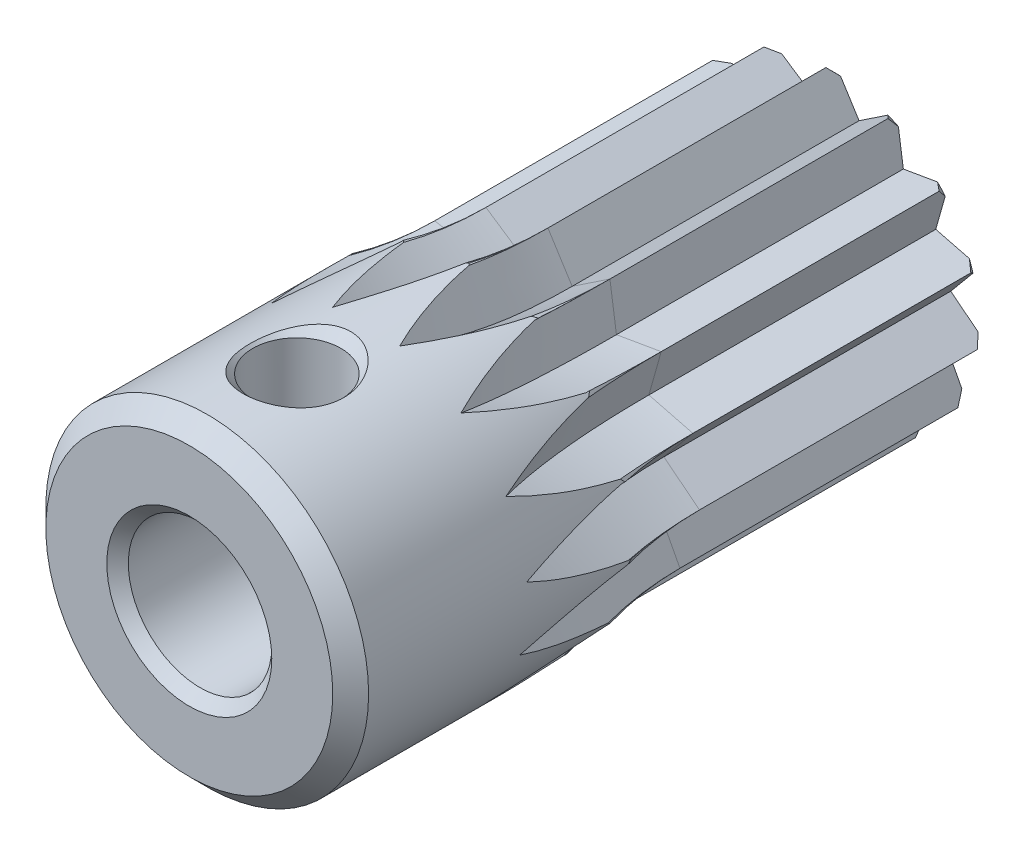
SolidWorks part; units mm, degrees
material "Delrin 2700 NC010, Low Viscosity Acetal Copolymer (SS)"
ref_plane "Front Plane" through (0, 0, 0) normal (0, 0, 1) x (1, 0, 0)
ref_plane "Top Plane" through (0, 0, 0) normal (0, 1, 0) x (1, 0, 0)
ref_plane "Right Plane" through (0, 0, 0) normal (1, 0, 0) x (0, 0, -1)
ref_plane "Plane1" through (0, 0, 0) normal (1, 0, 0) x (0, 0, -1)
sketch "Sketch1" plane through (0, 0, 0) normal (1, 0, 0) x (0, 0, -1)
  line L0 (-18, 2.3) -> (-17.7, 2)
  line L1 (-17.7, 2) -> (-0.3, 2)
  line L2 (-0.3, 2) -> (0, 2.3)
  line L3 (0, 2.3) -> (0, 4)
  line L4 (0, 4) -> (-0.5, 4.5)
  line L5 (-0.5, 4.5) -> (-17.5, 4.5)
  line L6 (-17.5, 4.5) -> (-18, 4)
  line L7 (-18, 4) -> (-18, 2.3)
  line L8 (0, 0) -> (-18, 0) construction
revolve "Revolve1" add sketch "Sketch1" angle 360 about L8
ref_plane "Plane2" through (0, 0, 8) normal (0, 0, 1) x (1, 0, 0)
sketch "Sketch2" plane through (0, 0, 8) normal (0, 0, 1) x (1, 0, 0)
  line L0 (-4.2267, -0.4442) -> (-3.0909, -1.0043)
  line L1 (-3.0909, -1.0043) -> (-3.6806, -2.125)
  line L2 (-3.6806, -2.125) -> (-2.4152, -2.1747)
  line L3 (-2.4152, -2.1747) -> (-2.4981, -3.4383)
  line L4 (-2.4981, -3.4383) -> (-1.3219, -2.969)
  line L5 (-1.3219, -2.969) -> (-0.8836, -4.1571)
  line L6 (-0.8836, -4.1571) -> (0, -3.25)
  line L7 (0, -3.25) -> (0.8836, -4.1571)
  line L8 (0.8836, -4.1571) -> (1.3219, -2.969)
  line L9 (1.3219, -2.969) -> (2.4981, -3.4383)
  line L10 (2.4981, -3.4383) -> (2.4152, -2.1747)
  line L11 (2.4152, -2.1747) -> (3.6806, -2.125)
  line L12 (3.6806, -2.125) -> (3.0909, -1.0043)
  line L13 (3.0909, -1.0043) -> (4.2267, -0.4442)
  line L14 (4.2267, -0.4442) -> (3.2322, 0.3397)
  line L15 (3.2322, 0.3397) -> (4.042, 1.3133)
  line L16 (4.042, 1.3133) -> (2.8146, 1.625)
  line L17 (2.8146, 1.625) -> (3.1584, 2.8438)
  line L18 (3.1584, 2.8438) -> (1.9103, 2.6293)
  line L19 (1.9103, 2.6293) -> (1.7286, 3.8826)
  line L20 (1.7286, 3.8826) -> (0.6757, 3.179)
  line L21 (0.6757, 3.179) -> (0, 4.25)
  line L22 (0, 4.25) -> (-0.6757, 3.179)
  line L23 (-0.6757, 3.179) -> (-1.7286, 3.8826)
  line L24 (-1.7286, 3.8826) -> (-1.9103, 2.6293)
  line L25 (-1.9103, 2.6293) -> (-3.1584, 2.8438)
  line L26 (-3.1584, 2.8438) -> (-2.8146, 1.625)
  line L27 (-2.8146, 1.625) -> (-4.042, 1.3133)
  line L28 (-4.042, 1.3133) -> (-3.2322, 0.3397)
  line L29 (-3.2322, 0.3397) -> (-4.2267, -0.4442)
  circle A0 centre (0, 0) radius 8.5
extrude "Cut-Extrude1" cut sketch "Sketch2" against normal blind 8
ref_plane "Plane3" through (0, 0, 8) normal (0, 0, 1) x (1, 0, 0)
sketch "Sketch3" plane through (0, 0, 8) normal (0, 0, 1) x (1, 0, 0)
  line L0 (-2.0791, 14.0315) -> (0, 4.25)
  line L1 (0, 4.25) -> (-0.6757, 3.179)
  line L2 (-0.6757, 3.179) -> (-1.7286, 3.8826)
  line L3 (-1.7286, 3.8826) -> (-3.8077, 13.664)
  line L4 (-3.8077, 13.664) -> (-2.0791, 14.0315)
  line L5 (-3.8077, 13.664) -> (-2.0791, 14.0315) construction
revolve "Cut-Revolve1" cut sketch "Sketch3" angle 360 about L5
ref_plane "Plane4" through (0, 0, 8) normal (0, 0, 1) x (1, 0, 0)
sketch "Sketch4" plane through (0, 0, 8) normal (0, 0, 1) x (1, 0, 0)
  line L0 (3.8077, 13.664) -> (1.7286, 3.8826)
  line L1 (1.7286, 3.8826) -> (0.6757, 3.179)
  line L2 (0.6757, 3.179) -> (0, 4.25)
  line L3 (0, 4.25) -> (2.0791, 14.0315)
  line L4 (2.0791, 14.0315) -> (3.8077, 13.664)
  line L5 (2.0791, 14.0315) -> (3.8077, 13.664) construction
revolve "Cut-Revolve2" cut sketch "Sketch4" angle 360 about L5
ref_plane "Plane5" through (0, 0, 8) normal (0, 0, 1) x (1, 0, 0)
sketch "Sketch5" plane through (0, 0, 8) normal (0, 0, 1) x (1, 0, 0)
  line L0 (9.0362, 10.934) -> (3.1584, 2.8438)
  line L1 (3.1584, 2.8438) -> (1.9103, 2.6293)
  line L2 (1.9103, 2.6293) -> (1.7286, 3.8826)
  line L3 (1.7286, 3.8826) -> (7.6065, 11.9727)
  line L4 (7.6065, 11.9727) -> (9.0362, 10.934)
  line L5 (7.6065, 11.9727) -> (9.0362, 10.934) construction
revolve "Cut-Revolve3" cut sketch "Sketch5" angle 360 about L5
ref_plane "Plane6" through (0, 0, 8) normal (0, 0, 1) x (1, 0, 0)
sketch "Sketch6" plane through (0, 0, 8) normal (0, 0, 1) x (1, 0, 0)
  line L0 (12.7022, 6.3133) -> (4.042, 1.3133)
  line L1 (4.042, 1.3133) -> (2.8146, 1.625)
  line L2 (2.8146, 1.625) -> (3.1584, 2.8438)
  line L3 (3.1584, 2.8438) -> (11.8186, 7.8438)
  line L4 (11.8186, 7.8438) -> (12.7022, 6.3133)
  line L5 (11.8186, 7.8438) -> (12.7022, 6.3133) construction
revolve "Cut-Revolve4" cut sketch "Sketch6" angle 360 about L5
ref_plane "Plane7" through (0, 0, 8) normal (0, 0, 1) x (1, 0, 0)
sketch "Sketch7" plane through (0, 0, 8) normal (0, 0, 1) x (1, 0, 0)
  line L0 (14.1719, 0.601) -> (4.2267, -0.4442)
  line L1 (4.2267, -0.4442) -> (3.2322, 0.3397)
  line L2 (3.2322, 0.3397) -> (4.042, 1.3133)
  line L3 (4.042, 1.3133) -> (13.9872, 2.3586)
  line L4 (13.9872, 2.3586) -> (14.1719, 0.601)
  line L5 (13.9872, 2.3586) -> (14.1719, 0.601) construction
revolve "Cut-Revolve5" cut sketch "Sketch7" angle 360 about L5
ref_plane "Plane8" through (0, 0, 8) normal (0, 0, 1) x (1, 0, 0)
sketch "Sketch8" plane through (0, 0, 8) normal (0, 0, 1) x (1, 0, 0)
  line L0 (13.1912, -5.2152) -> (3.6806, -2.125)
  line L1 (3.6806, -2.125) -> (3.0909, -1.0043)
  line L2 (3.0909, -1.0043) -> (4.2267, -0.4442)
  line L3 (4.2267, -0.4442) -> (13.7373, -3.5344)
  line L4 (13.7373, -3.5344) -> (13.1912, -5.2152)
  line L5 (13.7373, -3.5344) -> (13.1912, -5.2152) construction
revolve "Cut-Revolve6" cut sketch "Sketch8" angle 360 about L5
ref_plane "Plane9" through (0, 0, 8) normal (0, 0, 1) x (1, 0, 0)
sketch "Sketch9" plane through (0, 0, 8) normal (0, 0, 1) x (1, 0, 0)
  line L0 (9.9295, -10.1296) -> (2.4981, -3.4383)
  line L1 (2.4981, -3.4383) -> (2.4152, -2.1747)
  line L2 (2.4152, -2.1747) -> (3.6806, -2.125)
  line L3 (3.6806, -2.125) -> (11.1121, -8.8163)
  line L4 (11.1121, -8.8163) -> (9.9295, -10.1296)
  line L5 (11.1121, -8.8163) -> (9.9295, -10.1296) construction
revolve "Cut-Revolve7" cut sketch "Sketch9" angle 360 about L5
ref_plane "Plane10" through (0, 0, 8) normal (0, 0, 1) x (1, 0, 0)
sketch "Sketch10" plane through (0, 0, 8) normal (0, 0, 1) x (1, 0, 0)
  line L0 (4.951, -13.2926) -> (0.8836, -4.1571)
  line L1 (0.8836, -4.1571) -> (1.3219, -2.969)
  line L2 (1.3219, -2.969) -> (2.4981, -3.4383)
  line L3 (2.4981, -3.4383) -> (6.5655, -12.5738)
  line L4 (6.5655, -12.5738) -> (4.951, -13.2926)
  line L5 (6.5655, -12.5738) -> (4.951, -13.2926) construction
revolve "Cut-Revolve8" cut sketch "Sketch10" angle 360 about L5
ref_plane "Plane11" through (0, 0, 8) normal (0, 0, 1) x (1, 0, 0)
sketch "Sketch11" plane through (0, 0, 8) normal (0, 0, 1) x (1, 0, 0)
  line L0 (-0.8836, -14.1571) -> (-0.8836, -4.1571)
  line L1 (-0.8836, -4.1571) -> (0, -3.25)
  line L2 (0, -3.25) -> (0.8836, -4.1571)
  line L3 (0.8836, -4.1571) -> (0.8836, -14.1571)
  line L4 (0.8836, -14.1571) -> (-0.8836, -14.1571)
  line L5 (0.8836, -14.1571) -> (-0.8836, -14.1571) construction
revolve "Cut-Revolve9" cut sketch "Sketch11" angle 360 about L5
ref_plane "Plane12" through (0, 0, 8) normal (0, 0, 1) x (1, 0, 0)
sketch "Sketch12" plane through (0, 0, 8) normal (0, 0, 1) x (1, 0, 0)
  line L0 (-6.5655, -12.5738) -> (-2.4981, -3.4383)
  line L1 (-2.4981, -3.4383) -> (-1.3219, -2.969)
  line L2 (-1.3219, -2.969) -> (-0.8836, -4.1571)
  line L3 (-0.8836, -4.1571) -> (-4.951, -13.2926)
  line L4 (-4.951, -13.2926) -> (-6.5655, -12.5738)
  line L5 (-4.951, -13.2926) -> (-6.5655, -12.5738) construction
revolve "Cut-Revolve10" cut sketch "Sketch12" angle 360 about L5
ref_plane "Plane13" through (0, 0, 8) normal (0, 0, 1) x (1, 0, 0)
sketch "Sketch13" plane through (0, 0, 8) normal (0, 0, 1) x (1, 0, 0)
  line L0 (-11.1121, -8.8163) -> (-3.6806, -2.125)
  line L1 (-3.6806, -2.125) -> (-2.4152, -2.1747)
  line L2 (-2.4152, -2.1747) -> (-2.4981, -3.4383)
  line L3 (-2.4981, -3.4383) -> (-9.9295, -10.1296)
  line L4 (-9.9295, -10.1296) -> (-11.1121, -8.8163)
  line L5 (-9.9295, -10.1296) -> (-11.1121, -8.8163) construction
revolve "Cut-Revolve11" cut sketch "Sketch13" angle 360 about L5
ref_plane "Plane14" through (0, 0, 8) normal (0, 0, 1) x (1, 0, 0)
sketch "Sketch14" plane through (0, 0, 8) normal (0, 0, 1) x (1, 0, 0)
  line L0 (-13.7373, -3.5344) -> (-4.2267, -0.4442)
  line L1 (-4.2267, -0.4442) -> (-3.0909, -1.0043)
  line L2 (-3.0909, -1.0043) -> (-3.6806, -2.125)
  line L3 (-3.6806, -2.125) -> (-13.1912, -5.2152)
  line L4 (-13.1912, -5.2152) -> (-13.7373, -3.5344)
  line L5 (-13.1912, -5.2152) -> (-13.7373, -3.5344) construction
revolve "Cut-Revolve12" cut sketch "Sketch14" angle 360 about L5
ref_plane "Plane15" through (0, 0, 8) normal (0, 0, 1) x (1, 0, 0)
sketch "Sketch15" plane through (0, 0, 8) normal (0, 0, 1) x (1, 0, 0)
  line L0 (-13.9872, 2.3586) -> (-4.042, 1.3133)
  line L1 (-4.042, 1.3133) -> (-3.2322, 0.3397)
  line L2 (-3.2322, 0.3397) -> (-4.2267, -0.4442)
  line L3 (-4.2267, -0.4442) -> (-14.1719, 0.601)
  line L4 (-14.1719, 0.601) -> (-13.9872, 2.3586)
  line L5 (-14.1719, 0.601) -> (-13.9872, 2.3586) construction
revolve "Cut-Revolve13" cut sketch "Sketch15" angle 360 about L5
ref_plane "Plane16" through (0, 0, 8) normal (0, 0, 1) x (1, 0, 0)
sketch "Sketch16" plane through (0, 0, 8) normal (0, 0, 1) x (1, 0, 0)
  line L0 (-11.8186, 7.8438) -> (-3.1584, 2.8438)
  line L1 (-3.1584, 2.8438) -> (-2.8146, 1.625)
  line L2 (-2.8146, 1.625) -> (-4.042, 1.3133)
  line L3 (-4.042, 1.3133) -> (-12.7022, 6.3133)
  line L4 (-12.7022, 6.3133) -> (-11.8186, 7.8438)
  line L5 (-12.7022, 6.3133) -> (-11.8186, 7.8438) construction
revolve "Cut-Revolve14" cut sketch "Sketch16" angle 360 about L5
ref_plane "Plane17" through (0, 0, 8) normal (0, 0, 1) x (1, 0, 0)
sketch "Sketch17" plane through (0, 0, 8) normal (0, 0, 1) x (1, 0, 0)
  line L0 (-7.6065, 11.9727) -> (-1.7286, 3.8826)
  line L1 (-1.7286, 3.8826) -> (-1.9103, 2.6293)
  line L2 (-1.9103, 2.6293) -> (-3.1584, 2.8438)
  line L3 (-3.1584, 2.8438) -> (-9.0362, 10.934)
  line L4 (-9.0362, 10.934) -> (-7.6065, 11.9727)
  line L5 (-9.0362, 10.934) -> (-7.6065, 11.9727) construction
revolve "Cut-Revolve15" cut sketch "Sketch17" angle 360 about L5
ref_plane "Plane18" through (0, 0, 8) normal (0, 0, 1) x (1, 0, 0)
sketch "Sketch18" plane through (0, 0, 8) normal (0, 0, 1) x (1, 0, 0)
  line L0 (-1.8835, 14.0731) -> (0.1956, 4.2916)
  line L1 (0.1956, 4.2916) -> (0, 4.25)
  line L2 (0, 4.25) -> (-0.6757, 3.179)
  line L3 (-0.6757, 3.179) -> (-1.7286, 3.8826)
  line L4 (-1.7286, 3.8826) -> (-1.9243, 3.841)
  line L5 (-1.9243, 3.841) -> (-4.0034, 13.6225)
  line L6 (-4.0034, 13.6225) -> (-1.8835, 14.0731)
  line L7 (-4.0034, 13.6225) -> (-1.8835, 14.0731) construction
revolve "Cut-Revolve16" cut sketch "Sketch18" angle 360 about L7
ref_plane "Plane19" through (0, 0, 8) normal (0, 0, 1) x (1, 0, 0)
sketch "Sketch19" plane through (0, 0, 8) normal (0, 0, 1) x (1, 0, 0)
  line L0 (4.0034, 13.6225) -> (1.9243, 3.841)
  line L1 (1.9243, 3.841) -> (1.7286, 3.8826)
  line L2 (1.7286, 3.8826) -> (0.6757, 3.179)
  line L3 (0.6757, 3.179) -> (0, 4.25)
  line L4 (0, 4.25) -> (-0.1956, 4.2916)
  line L5 (-0.1956, 4.2916) -> (1.8835, 14.0731)
  line L6 (1.8835, 14.0731) -> (4.0034, 13.6225)
  line L7 (1.8835, 14.0731) -> (4.0034, 13.6225) construction
revolve "Cut-Revolve17" cut sketch "Sketch19" angle 360 about L7
ref_plane "Plane20" through (0, 0, 8) normal (0, 0, 1) x (1, 0, 0)
sketch "Sketch20" plane through (0, 0, 8) normal (0, 0, 1) x (1, 0, 0)
  line L0 (12.8022, 6.1401) -> (4.142, 1.1401)
  line L1 (4.142, 1.1401) -> (4.042, 1.3133)
  line L2 (4.042, 1.3133) -> (2.8146, 1.625)
  line L3 (2.8146, 1.625) -> (3.1584, 2.8438)
  line L4 (3.1584, 2.8438) -> (3.0584, 3.017)
  line L5 (3.0584, 3.017) -> (11.7186, 8.017)
  line L6 (11.7186, 8.017) -> (12.8022, 6.1401)
  line L7 (11.7186, 8.017) -> (12.8022, 6.1401) construction
revolve "Cut-Revolve18" cut sketch "Sketch20" angle 360 about L7
ref_plane "Plane21" through (0, 0, 8) normal (0, 0, 1) x (1, 0, 0)
sketch "Sketch21" plane through (0, 0, 8) normal (0, 0, 1) x (1, 0, 0)
  line L0 (13.1294, -5.4054) -> (3.6188, -2.3152)
  line L1 (3.6188, -2.3152) -> (3.6806, -2.125)
  line L2 (3.6806, -2.125) -> (3.0909, -1.0043)
  line L3 (3.0909, -1.0043) -> (4.2267, -0.4442)
  line L4 (4.2267, -0.4442) -> (4.2885, -0.254)
  line L5 (4.2885, -0.254) -> (13.7991, -3.3442)
  line L6 (13.7991, -3.3442) -> (13.1294, -5.4054)
  line L7 (13.7991, -3.3442) -> (13.1294, -5.4054) construction
revolve "Cut-Revolve19" cut sketch "Sketch21" angle 360 about L7
ref_plane "Plane22" through (0, 0, 8) normal (0, 0, 1) x (1, 0, 0)
sketch "Sketch22" plane through (0, 0, 8) normal (0, 0, 1) x (1, 0, 0)
  line L0 (4.7683, -13.3739) -> (0.7009, -4.2385)
  line L1 (0.7009, -4.2385) -> (0.8836, -4.1571)
  line L2 (0.8836, -4.1571) -> (1.3219, -2.969)
  line L3 (1.3219, -2.969) -> (2.4981, -3.4383)
  line L4 (2.4981, -3.4383) -> (2.6808, -3.357)
  line L5 (2.6808, -3.357) -> (6.7482, -12.4924)
  line L6 (6.7482, -12.4924) -> (4.7683, -13.3739)
  line L7 (6.7482, -12.4924) -> (4.7683, -13.3739) construction
revolve "Cut-Revolve20" cut sketch "Sketch22" angle 360 about L7
ref_plane "Plane23" through (0, 0, 8) normal (0, 0, 1) x (1, 0, 0)
sketch "Sketch23" plane through (0, 0, 8) normal (0, 0, 1) x (1, 0, 0)
  line L0 (-6.7482, -12.4924) -> (-2.6808, -3.357)
  line L1 (-2.6808, -3.357) -> (-2.4981, -3.4383)
  line L2 (-2.4981, -3.4383) -> (-1.3219, -2.969)
  line L3 (-1.3219, -2.969) -> (-0.8836, -4.1571)
  line L4 (-0.8836, -4.1571) -> (-0.7009, -4.2385)
  line L5 (-0.7009, -4.2385) -> (-4.7683, -13.3739)
  line L6 (-4.7683, -13.3739) -> (-6.7482, -12.4924)
  line L7 (-4.7683, -13.3739) -> (-6.7482, -12.4924) construction
revolve "Cut-Revolve21" cut sketch "Sketch23" angle 360 about L7
ref_plane "Plane24" through (0, 0, 8) normal (0, 0, 1) x (1, 0, 0)
sketch "Sketch24" plane through (0, 0, 8) normal (0, 0, 1) x (1, 0, 0)
  line L0 (-13.7991, -3.3442) -> (-4.2885, -0.254)
  line L1 (-4.2885, -0.254) -> (-4.2267, -0.4442)
  line L2 (-4.2267, -0.4442) -> (-3.0909, -1.0043)
  line L3 (-3.0909, -1.0043) -> (-3.6806, -2.125)
  line L4 (-3.6806, -2.125) -> (-3.6188, -2.3152)
  line L5 (-3.6188, -2.3152) -> (-13.1294, -5.4054)
  line L6 (-13.1294, -5.4054) -> (-13.7991, -3.3442)
  line L7 (-13.1294, -5.4054) -> (-13.7991, -3.3442) construction
revolve "Cut-Revolve22" cut sketch "Sketch24" angle 360 about L7
ref_plane "Plane25" through (0, 0, 8) normal (0, 0, 1) x (1, 0, 0)
sketch "Sketch25" plane through (0, 0, 8) normal (0, 0, 1) x (1, 0, 0)
  line L0 (-11.7186, 8.017) -> (-3.0584, 3.017)
  line L1 (-3.0584, 3.017) -> (-3.1584, 2.8438)
  line L2 (-3.1584, 2.8438) -> (-2.8146, 1.625)
  line L3 (-2.8146, 1.625) -> (-4.042, 1.3133)
  line L4 (-4.042, 1.3133) -> (-4.142, 1.1401)
  line L5 (-4.142, 1.1401) -> (-12.8022, 6.1401)
  line L6 (-12.8022, 6.1401) -> (-11.7186, 8.017)
  line L7 (-12.8022, 6.1401) -> (-11.7186, 8.017) construction
revolve "Cut-Revolve23" cut sketch "Sketch25" angle 360 about L7
ref_plane "Plane26" through (0, 0, 15) normal (0, 0, 1) x (1, 0, 0)
sketch "Sketch26" plane through (0, 0, 15) normal (0, 0, 1) x (1, 0, 0)
  line L0 (0, 0) -> (-1.5, 0)
  line L1 (-1.5, 0) -> (-1.5, 2)
  line L2 (-1.5, 2) -> (-1.2295, 2.2705)
  line L3 (-1.2295, 2.2705) -> (-1.2295, 4.2295)
  line L4 (-1.2295, 4.2295) -> (-1.5, 4.5)
  line L5 (-1.5, 4.5) -> (-1.5, 8.5)
  line L6 (-1.5, 8.5) -> (0, 8.5)
  line L7 (0, 8.5) -> (0, 0)
  line L8 (0, 8.5) -> (0, 0) construction
revolve "Cut-Revolve24" cut sketch "Sketch26" angle 360 about L8
